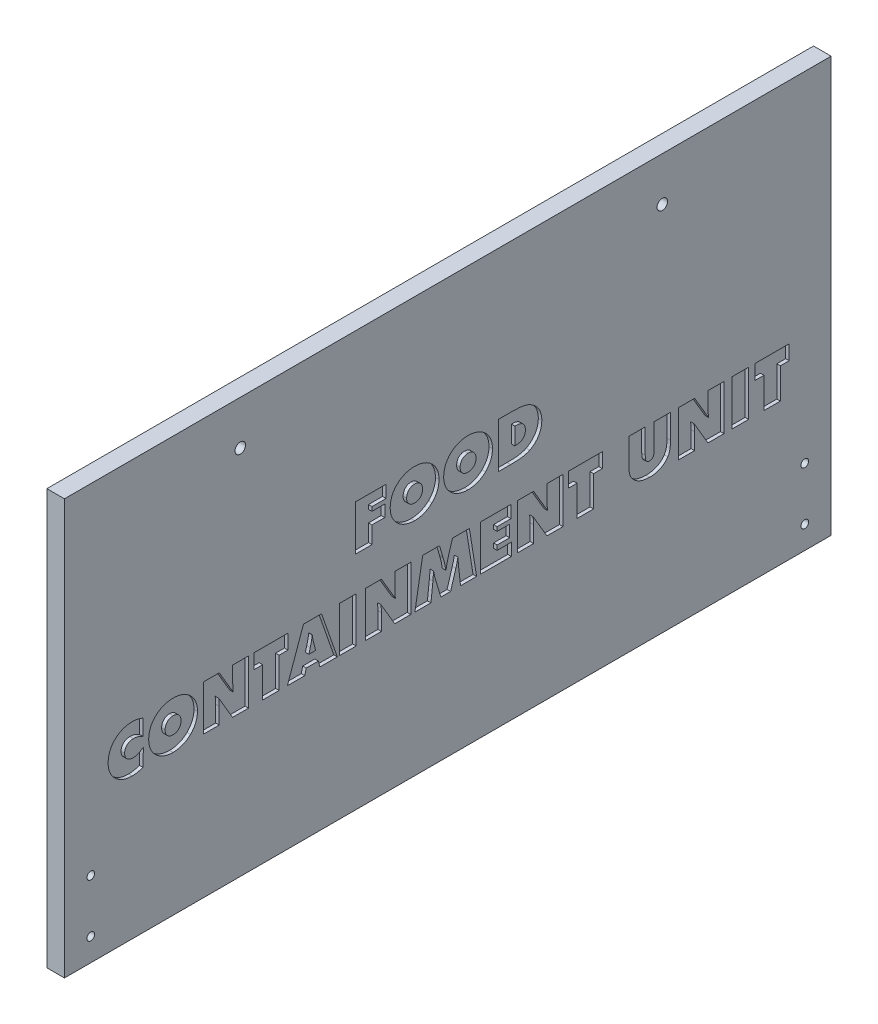
SolidWorks part; units mm, degrees
ref_plane "Front Plane" through (0, 0, 0) normal (0, 0, 1) x (1, 0, 0)
ref_plane "Top Plane" through (0, 0, 0) normal (0, 1, 0) x (1, 0, 0)
ref_plane "Right Plane" through (0, 0, 0) normal (1, 0, 0) x (0, 0, -1)
sketch "Sketch2" plane through (0, 0, 0) normal (1, 0, 0) x (0, 0, -1)
  line L1 (0, 0) -> (218, 0)
  line L2 (0, 0) -> (0, 118)
  line L3 (0, 118) -> (218, 118)
  line L4 (218, 0) -> (218, 118)
  dimension "D1" = 218
  dimension "D2" = 118
extrude "Boss-Extrude1" add sketch "Sketch2" against normal blind 5
sketch "Sketch14" plane through (0, 0, 0) normal (1, 0, 0) x (0, 0, -1)
  line L0 (0, 63) -> (218, 63) construction
  line L1 (0, 118) -> (0, 0) construction
  line L2 (218, 0) -> (218, 118) construction
  line L3 (218, 118) -> (0, 118) construction
  dimension "D1" = 55
sketch "Sketch15" plane through (0, 0, 0) normal (1, 0, 0) x (0, 0, -1)
  text T0 "FOOD\r\nCONTAINMENT UNIT" font "Futura XBlk BT" height in points 48
extrude "Cut-Extrude2" cut sketch "Sketch15" against normal blind 1
sketch "Sketch16" plane through (0, 0, 0) normal (1, 0, 0) x (0, 0, -1)
  line L0 (0, 118) -> (0, 0) construction
  line L1 (218, 118) -> (0, 118) construction
  circle A0 centre (50, 105.5) radius 1.5
  circle A1 centre (170, 105.5) radius 1.5
  dimension "D1" = 3
  dimension "D2" = 3
  dimension "D3" = 120
  dimension "D4" = 50
  dimension "D5" = 12.5
  dimension "D6" = 12.5
extrude "Cut-Extrude3" cut sketch "Sketch16" against normal through all
sketch "Sketch18" plane through (0, 0, 0) normal (1, 0, 0) x (0, 0, -1)
  line L0 (0, 118) -> (0, 0) construction
  line L1 (0, 0) -> (218, 0) construction
  circle A0 centre (7.5, 21.5) radius 1.1
  circle A1 centre (7.5, 6.5) radius 1.1
  dimension "D4" = 2.2
  dimension "D5" = 2.2
  dimension "D1" = 7.5
  dimension "D2" = 7.5
  dimension "D3" = 6.5
  dimension "D6" = 15
extrude "Cut-Extrude4" cut sketch "Sketch18" against normal through all
ref_plane "Plane3" through (0, 0, -109) normal (0, 0, 1) x (1, 0, 0)
mirror "Mirror1" about plane through (0, 0, -109) normal (0, 0, 1) of "Cut-Extrude4"
